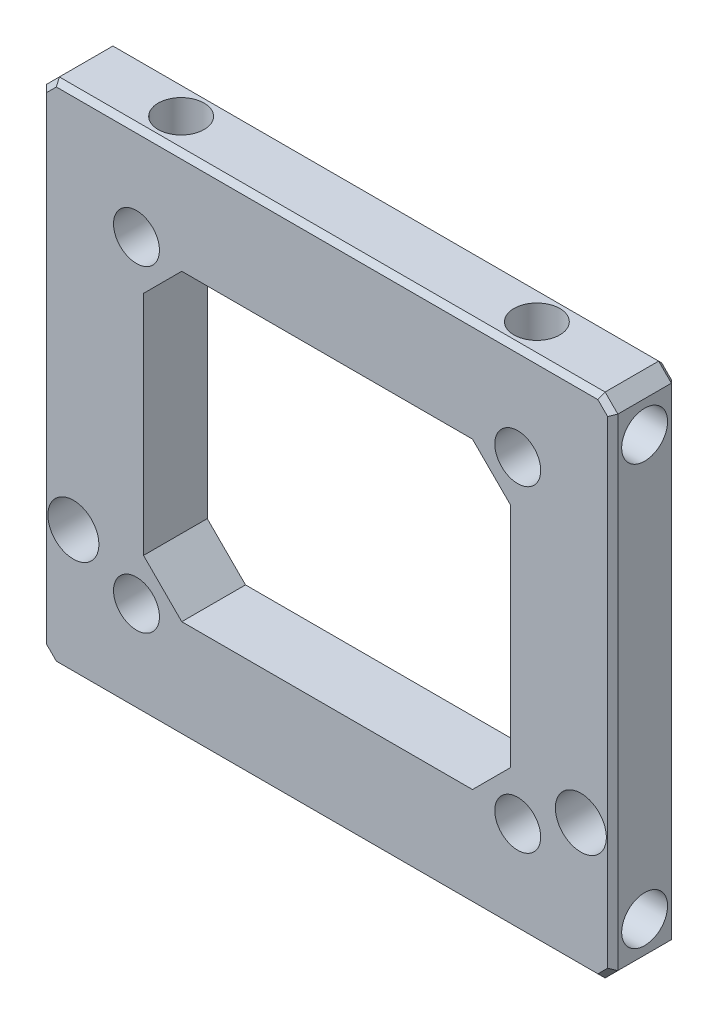
SolidWorks part; units mm, degrees
ref_plane "Front Plane" through (0, 0, 0) normal (0, 0, 1) x (1, 0, 0)
ref_plane "Top Plane" through (0, 0, 0) normal (0, 1, 0) x (1, 0, 0)
ref_plane "Right Plane" through (0, 0, 0) normal (1, 0, 0) x (0, 0, -1)
sketch "Sketch2" plane through (0, 0, 0) normal (0, 0, 1) x (1, 0, 0)
  line L0 (-22.4, 0) -> (22.4, 0) construction
  line L1 (-22.4, 19.9) -> (22.4, 19.9)
  line L2 (-22.4, 19.9) -> (-22.4, -19.9)
  line L3 (-22.4, -19.9) -> (22.4, -19.9)
  line L4 (22.4, 19.9) -> (22.4, -19.9)
  line L5 (0, 11.9) -> (0, -11.9) construction
  line L6 (-14.4, 11.9) -> (14.4, 11.9)
  line L7 (-14.4, 11.9) -> (-14.4, -11.9)
  line L8 (-14.4, -11.9) -> (14.4, -11.9)
  line L9 (14.4, 11.9) -> (14.4, -11.9)
  point P6 (0, 0)
  point P14 (0, 0)
  dimension "D1" = 44.8
  dimension "D2" = 39.8
  dimension "D3" = 8
  dimension "D4" = 8
extrude "Boss-Extrude1" add sketch "Sketch2" along normal blind 5
chamfer "Chamfer1" distance 1 angle 45 4 edges at (-22.4, -19.9, 2.5) (22.4, -19.9, 2.5) (22.4, 19.9, 2.5) (-22.4, 19.9, 2.5)
chamfer "Chamfer2" distance 3 angle 45 4 edges at (-14.4, -11.9, 2.5) (14.4, -11.9, 2.5) (14.4, 11.9, 2.5) (-14.4, 11.9, 2.5)
sketch "Sketch3" plane through (0, 0, 5) normal (0, 0, 1) x (1, 0, 0)
  line L0 (21.4, 19.9) -> (-21.4, 19.9) construction
  line L1 (22.4, -18.9) -> (22.4, 18.9) construction
  circle A0 centre (14.95, 12.45) radius 1.8
  dimension "D1" = 3.6
  dimension "D2" = 7.45
  dimension "D3" = 7.45
extrude "Cut-Extrude1" cut sketch "Sketch3" against normal through all
sketch "Sketch4" plane through (0, 19.9, 0) normal (0, 1, 0) x (1, 0, 0)
  line L0 (21.4, -5) -> (-21.4, -5) construction
  line L1 (22.4, 0) -> (22.4, -5) construction
  circle A0 centre (13.95, -2.5) radius 1.8
  dimension "D1" = 3.6
  dimension "D2" = 2.5
  dimension "D3" = 8.45
extrude "Cut-Extrude2" cut sketch "Sketch4" against normal blind 5
sketch "Sketch5" plane through (22.4, 0, 0) normal (1, 0, 0) x (0, 0, -1)
  line L0 (-5, -18.9) -> (-5, 18.9) construction
  line L1 (-5, 19.9) -> (0, 19.9) construction
  circle A0 centre (-2.5, 16.45) radius 1.8
  dimension "D2" = 3.6
  dimension "D3" = 3.45
  dimension "D1" = 2.5
extrude "Cut-Extrude3" cut sketch "Sketch5" against normal blind 5
mirror "Mirror1" about plane through (0, 0, 0) normal (0, 1, 0) of "Cut-Extrude3", "Cut-Extrude2", "Cut-Extrude1"
mirror "Mirror2" about plane through (0, 0, 0) normal (1, 0, 0) of "Mirror1", "Cut-Extrude1", "Cut-Extrude2", "Cut-Extrude3"
sketch "Sketch6" plane through (0, 0, 5) normal (0, 0, 1) x (1, 0, 0)
  line L0 (19.9, -9.9) -> (-19.9, -9.9) construction
  line L1 (22.4, -18.9) -> (22.4, 18.9) construction
  line L2 (-22.4, 18.9) -> (-22.4, -18.9) construction
  line L3 (-21.4, -19.9) -> (21.4, -19.9) construction
  circle A0 centre (19.9, -9.9) radius 2
  circle A1 centre (-19.9, -9.9) radius 2
  dimension "D1" = 4
  dimension "D2" = 4
  dimension "D4" = 2.5
  dimension "D3" = 2.5
  dimension "D5" = 10
extrude "Cut-Extrude4" cut sketch "Sketch6" against normal through all
chamfer "Chamfer3" distance 0.4 angle 45 16 edges at (21.9, -19.4, 0) (0, -19.9, 0) (-21.9, -19.4, 0) (-22.4, 0, 0) (-21.9, 19.4, 0) (0, 19.9, 0) (21.9, 19.4, 0) (22.4, 0, 0) (21.9, -19.4, 5) (0, -19.9, 5) (-21.9, -19.4, 5) (-22.4, 0, 5) (-21.9, 19.4, 5) (0, 19.9, 5) (21.9, 19.4, 5) (22.4, 0, 5)
